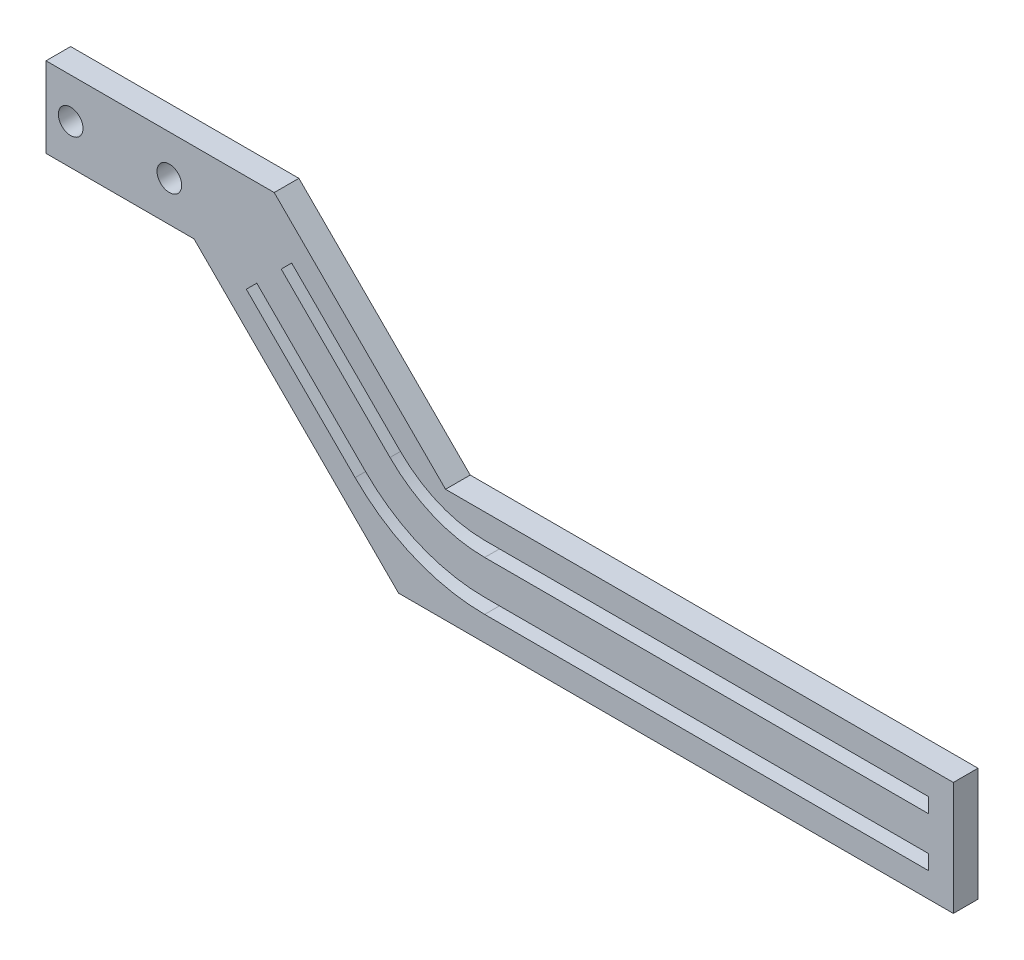
SolidWorks part; units mm, degrees
ref_plane "Front Plane" through (0, 0, 0) normal (0, 0, 1) x (1, 0, 0)
ref_plane "Top Plane" through (0, 0, 0) normal (0, 1, 0) x (1, 0, 0)
ref_plane "Right Plane" through (0, 0, 0) normal (1, 0, 0) x (0, 0, -1)
sketch "Sketch2" plane through (0, 0, 0) normal (0, 0, 1) x (1, 0, 0)
  line L18 (-27.8787, 32.1213) -> (-5.8284, 10.0711)
  line L25 (1.2426, 3) -> (11.2426, 3) construction
  line L26 (101.2426, 3) -> (101.2426, 0)
  line L27 (101.2426, 0) -> (11.2426, 0)
  line L28 (0, 0) -> (-7.9497, 7.9497) construction
  line L29 (-30, 30) -> (-27.8787, 32.1213)
  line L30 (-34.9497, 25.0503) -> (-12.8995, 3)
  line L31 (-2.8995, -7) -> (11.2426, -7) construction
  line L32 (101.2426, -10) -> (11.2426, -10)
  line L33 (-4.1421, -10) -> (-15.0208, 0.8787) construction
  line L34 (-37.0711, 22.9289) -> (-34.9497, 25.0503)
  line L35 (101.2426, -7) -> (101.2426, -10)
  line L36 (-47.6777, 26.4645) -> (-31.4142, 42.7279) construction
  line L37 (-31.4142, 42.7279) -> (3.3137, 8)
  line L38 (3.3137, 8) -> (106.2426, 8)
  line L39 (106.2426, 8) -> (106.2426, -15)
  line L40 (106.2426, -15) -> (-6.2132, -15)
  line L41 (-6.2132, -15) -> (-47.6777, 26.4645)
  line L42 (11.2426, 3) -> (11.2426, -10) construction
  line L43 (-5.8284, 10.0711) -> (-15.0208, 0.8787) construction
  line L44 (-5.8284, 10.0711) -> (1.2426, 3) construction
  line L45 (-27.8787, 32.1213) -> (1.2426, 3) construction
  line L46 (11.2426, 3) -> (101.2426, 3)
  line L47 (1.2426, 3) -> (101.2426, 3) construction
  line L48 (11.2426, 0) -> (0, 0) construction
  line L49 (101.2426, 0) -> (0, 0) construction
  line L50 (-7.9497, 7.9497) -> (-30, 30)
  line L51 (0, 0) -> (-30, 30) construction
  line L52 (-12.8995, 3) -> (-2.8995, -7) construction
  line L53 (-34.9497, 25.0503) -> (-2.8995, -7) construction
  line L54 (-15.0208, 0.8787) -> (-37.0711, 22.9289)
  line L55 (-4.1421, -10) -> (-37.0711, 22.9289) construction
  line L56 (11.2426, -10) -> (-4.1421, -10) construction
  line L57 (101.2426, -10) -> (-4.1421, -10) construction
  line L58 (11.2426, -7) -> (101.2426, -7)
  line L59 (-2.8995, -7) -> (101.2426, -7) construction
  line L60 (-39.5459, 34.5962) -> (-77.6777, 34.5962) construction
  line L61 (-31.4142, 42.7279) -> (-77.6777, 42.7279)
  line L62 (-77.6777, 42.7279) -> (-77.6777, 26.4645)
  line L63 (-77.6777, 26.4645) -> (-47.6777, 26.4645)
  arc A0 (11.2426, 3) -> (-5.8284, 10.0711) centre (11.2426, 27.1421) cw
  arc A1 (11.2426, 0) -> (-7.9497, 7.9497) centre (11.2426, 27.1421) cw
  arc A2 (-12.8995, 3) -> (11.2426, -7) centre (11.2426, 27.1421) ccw
  arc A3 (11.2426, -10) -> (-15.0208, 0.8787) centre (11.2426, 27.1421) cw
  circle A5 centre (-72.6777, 34.5962) radius 2.5
  circle A6 centre (-52.6777, 34.5962) radius 2.5
  point P15 (11.2426, 3)
  point P19 (-5.8284, 10.0711)
  dimension "D16" = 5
  dimension "D17" = 20
  dimension "D19" = 5
  dimension "D1" = 3
  dimension "D2" = 3
  dimension "D3" = 100
  dimension "D4" = 30
  dimension "D5" = 135
  dimension "D6" = 10
  dimension "D7" = 10
  dimension "D8" = 5
  dimension "D9" = 5
  dimension "D10" = 5
  dimension "D11" = 5
  dimension "D12" = 5
  dimension "D13" = 10
  dimension "D14" = 10
  dimension "D15" = 10
  dimension "D18" = 30
extrude "Boss-Extrude1" add sketch "Sketch2" along normal blind 5
sketch "Sketch3" plane through (0, 0, 5) normal (0, 0, 1) x (1, 0, 0)
  line L0 (-12.8995, 3) -> (-34.9497, 25.0503) construction
  line L1 (101.2426, -7) -> (11.2426, -7) construction
  line L2 (101.2426, 3) -> (11.2426, 3) construction
  line L3 (-5.8284, 10.0711) -> (-27.8787, 32.1213) construction
  line L4 (-12.8995, 3) -> (-34.9497, 25.0503)
  line L5 (101.2426, -7) -> (11.2426, -7)
  line L6 (101.2426, 3) -> (11.2426, 3)
  line L7 (-5.8284, 10.0711) -> (-27.8787, 32.1213)
  line L8 (101.2426, 1.5) -> (11.2426, 1.5)
  line L9 (-6.8891, 9.0104) -> (-28.9393, 31.0607)
  line L10 (101.2426, -8.5) -> (11.2426, -8.5)
  line L11 (-13.9602, 1.9393) -> (-36.0104, 23.9896)
  arc A0 (-12.8995, 3) -> (11.2426, -7) centre (11.2426, 27.1421) ccw construction
  arc A1 (-5.8284, 10.0711) -> (11.2426, 3) centre (11.2426, 27.1421) ccw construction
  arc A2 (-12.8995, 3) -> (11.2426, -7) centre (11.2426, 27.1421) ccw
  arc A3 (-5.8284, 10.0711) -> (11.2426, 3) centre (11.2426, 27.1421) ccw
  arc A4 (-6.8891, 9.0104) -> (11.2426, 1.5) centre (11.2426, 27.1421) ccw
  arc A5 (-13.9602, 1.9393) -> (11.2426, -8.5) centre (11.2426, 27.1421) ccw
  dimension "D1" = 1.5
sketch "Sketch4" plane through (0, 0, 0) normal (0, 0, -1) x (-1, 0, 0)
  line L0 (-101.2426, -8.5) -> (-11.2426, -8.5) construction
  line L1 (13.9602, 1.9393) -> (36.0104, 23.9896) construction
  line L2 (6.8891, 9.0104) -> (28.9393, 31.0607) construction
  line L3 (-101.2426, 1.5) -> (-11.2426, 1.5) construction
  line L4 (-101.2426, -8.5) -> (-11.2426, -8.5)
  line L5 (13.9602, 1.9393) -> (36.0104, 23.9896)
  line L6 (6.8891, 9.0104) -> (28.9393, 31.0607)
  line L7 (-101.2426, 1.5) -> (-11.2426, 1.5)
  line L8 (-101.2426, -3.5) -> (-11.2426, -3.5)
  line L9 (10.4246, 5.4749) -> (32.4749, 27.5251)
  arc A0 (-11.2426, -8.5) -> (13.9602, 1.9393) centre (-11.2426, 27.1421) ccw construction
  arc A1 (-11.2426, 1.5) -> (6.8891, 9.0104) centre (-11.2426, 27.1421) ccw construction
  arc A2 (-11.2426, -8.5) -> (13.9602, 1.9393) centre (-11.2426, 27.1421) ccw
  arc A3 (-11.2426, 1.5) -> (6.8891, 9.0104) centre (-11.2426, 27.1421) ccw
  arc A4 (-11.2426, -3.5) -> (10.4246, 5.4749) centre (-11.2426, 27.1421) ccw
  dimension "D1" = 5
